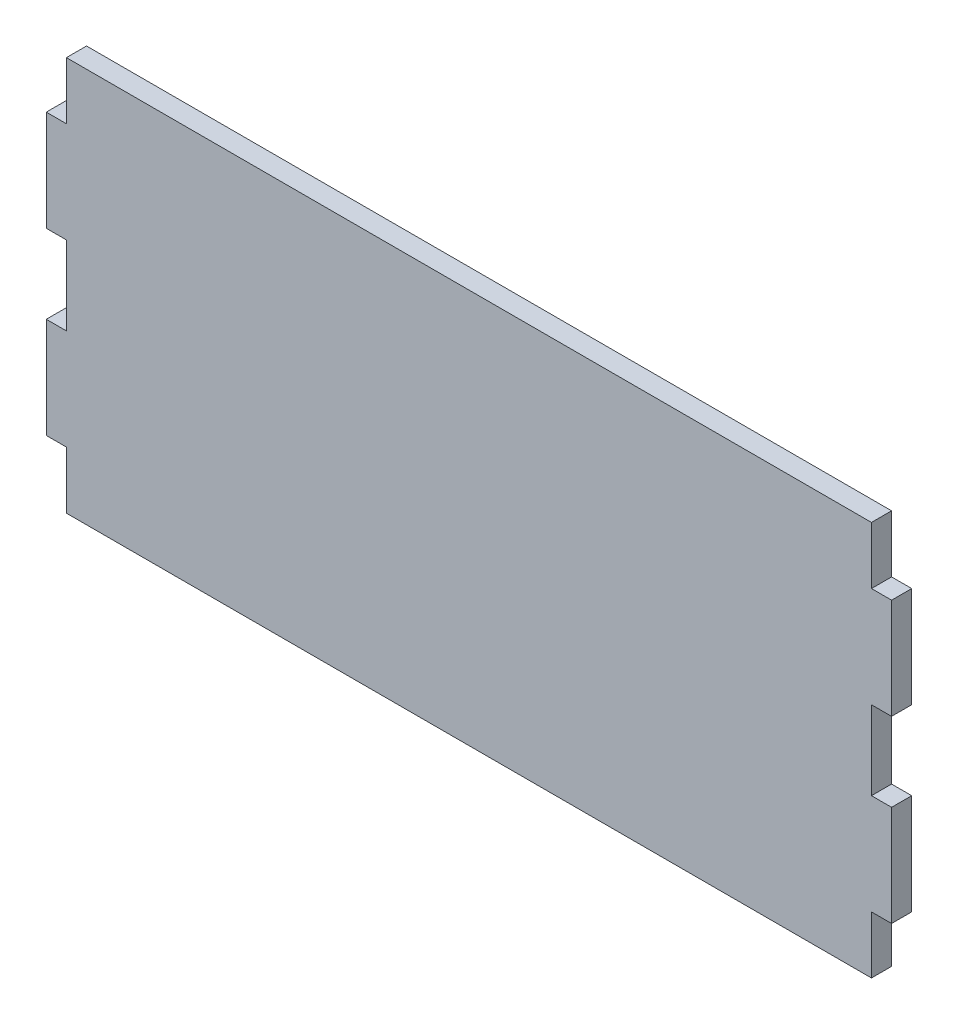
SolidWorks part; units mm, degrees
ref_plane "Alzado" through (0, 0, 0) normal (0, 0, 1) x (1, 0, 0)
ref_plane "Planta" through (0, 0, 0) normal (0, 1, 0) x (1, 0, 0)
ref_plane "Vista lateral" through (0, 0, 0) normal (1, 0, 0) x (0, 0, -1)
sketch "Sketch1" plane through (0, 0, 0) normal (0, 0, 1) x (1, 0, 0)
  line L0 (0, 0) -> (600, 0)
  line L1 (600, 0) -> (600, 42.675)
  line L2 (600, 42.675) -> (615, 42.675)
  line L3 (615, 42.675) -> (615, 117.675)
  line L4 (615, 117.675) -> (600, 117.675)
  line L5 (600, 117.675) -> (600, 176.375)
  line L6 (600, 176.375) -> (615, 176.375)
  line L7 (615, 176.375) -> (615, 251.375)
  line L8 (615, 251.375) -> (600, 251.375)
  line L9 (600, 251.375) -> (600, 294.05)
  line L10 (300, 439.6261) -> (300, -97.979) construction
  line L11 (600, 294.05) -> (0, 294.05)
  line L12 (-15, 117.675) -> (0, 117.675)
  line L13 (-15, 42.675) -> (-15, 117.675)
  line L14 (0, 42.675) -> (-15, 42.675)
  line L15 (0, 0) -> (0, 42.675)
  line L16 (0, 117.675) -> (0, 176.375)
  line L17 (0, 176.375) -> (-15, 176.375)
  line L18 (-15, 176.375) -> (-15, 251.375)
  line L19 (-15, 251.375) -> (0, 251.375)
  line L20 (0, 251.375) -> (0, 294.05)
  dimension "D1" = 600
  dimension "D2" = 15
  dimension "D3" = 294.05
  dimension "D4" = 75
  dimension "D5" = 58.7
extrude "Boss-Extrude1" add sketch "Sketch1" along normal blind 15
